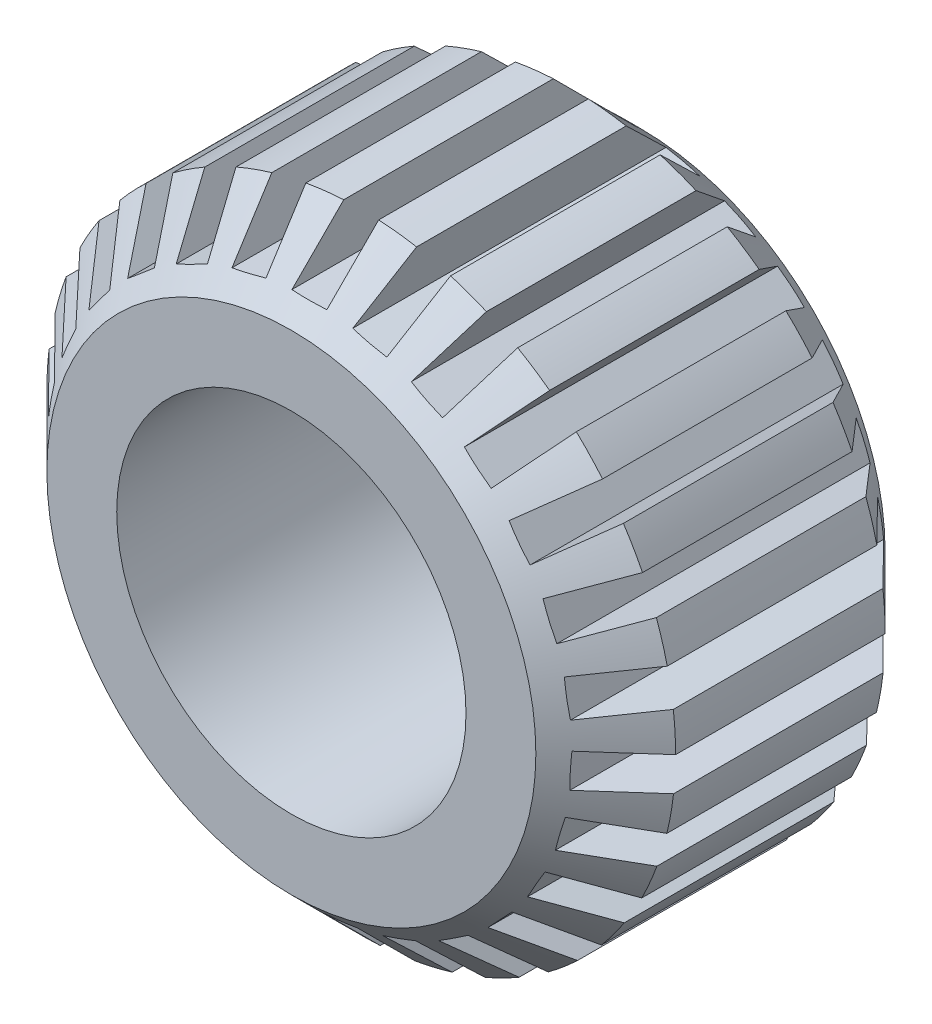
SolidWorks part; units mm, degrees
material "BUTYL"
ref_plane "Front Plane" through (0, 0, 0) normal (0, 0, 1) x (1, 0, 0)
ref_plane "Top Plane" through (0, 0, 0) normal (0, 1, 0) x (1, 0, 0)
ref_plane "Right Plane" through (0, 0, 0) normal (1, 0, 0) x (0, 0, -1)
sketch "Sketch1" plane through (0, 0, 0) normal (0, 0, 1) x (1, 0, 0)
  circle A0 centre (0, 0) radius 5
  circle A1 centre (0, 0) radius 9
  dimension "D1" = 10
  dimension "D2" = 4
extrude "Boss-Extrude1" add sketch "Sketch1" along normal blind 10
chamfer "Chamfer1" distance 2 angle 45 2 edges at (9, 0, 0) (9, 0, 10)
sketch "Sketch2" plane through (0, 0, 0) normal (0, 0, 1) x (1, 0, 0)
  line L0 (0, 0) -> (0, 9) construction
  line L1 (0.5, 7.5) -> (0.5, 8.9861)
  line L2 (-0.5, 7.5) -> (-0.5, 8.9861)
  line L3 (-0.5, 7.5) -> (0.5, 7.5)
  line L4 (-0.5, 0) -> (-0.5, 9) construction
  line L5 (0.5, 0) -> (0.5, 9) construction
  circle A0 centre (0, 0) radius 9 construction
  arc A1 (0.5, 8.9861) -> (-0.5, 8.9861) centre (0, 0) ccw
  dimension "D3" = 7.5
  dimension "D1" = 0.5
  dimension "D2" = 0.5
extrude "Cut-Extrude1" cut sketch "Sketch2" along normal through all
pattern_circular "CirPattern1" count 27 over 360 about axis through (0, 0, 0) along (0, 0, 1) of "Cut-Extrude1"
